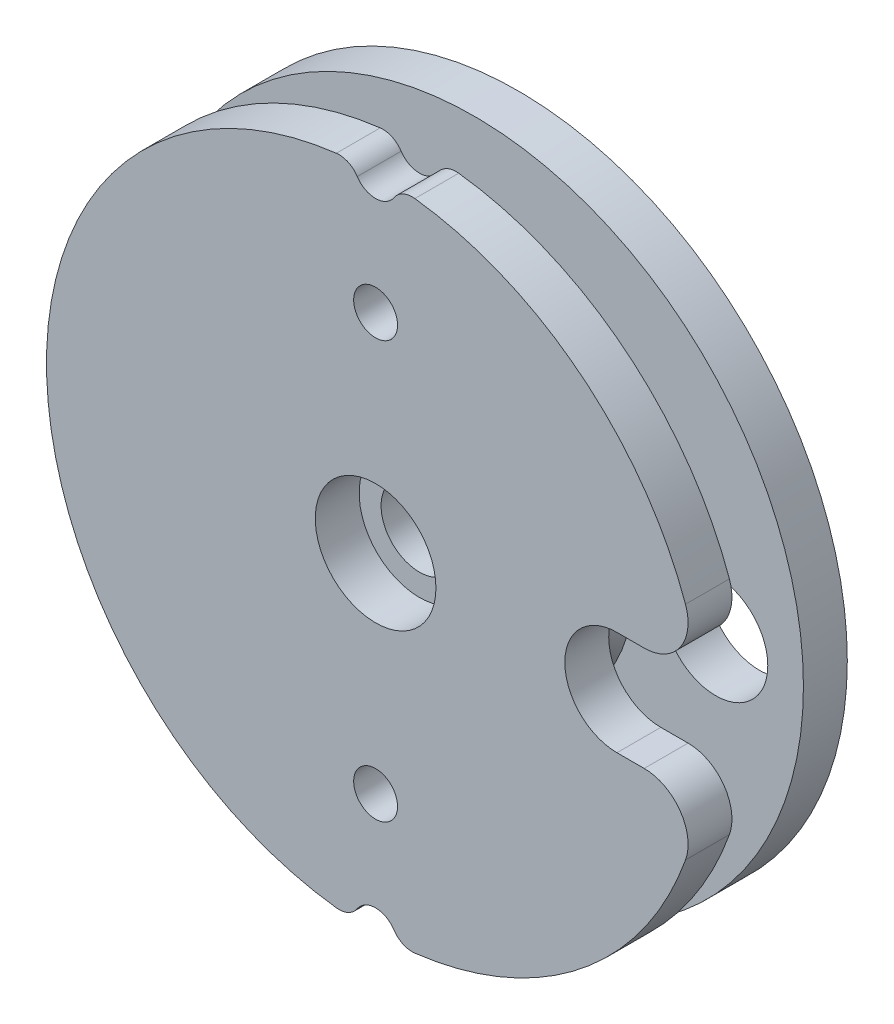
SolidWorks part; units mm, degrees
material "ABS"
ref_plane "Front Plane" through (0, 0, 0) normal (0, 0, 1) x (1, 0, 0)
ref_plane "Top Plane" through (0, 0, 0) normal (0, 1, 0) x (1, 0, 0)
ref_plane "Right Plane" through (0, 0, 0) normal (1, 0, 0) x (0, 0, -1)
sketch "Sketch1" plane through (0, 0, 0) normal (0, 0, 1) x (1, 0, 0)
  circle A0 centre (0, 0) radius 15
  dimension "D1" = 30
extrude "Body" add sketch "Sketch1" along normal mid plane 6.5
sketch "Sketch2" plane through (0, 0, 0) normal (0, 0, 1) x (1, 0, 0)
  circle A0 centre (0, 0) radius 15
  circle A1 centre (0, 0) radius 6.5
  circle A2 centre (0, 0) radius 15 construction
  dimension "D1" = 13
extrude "Pulley Clearance" cut sketch "Sketch2" against normal mid plane 2.5
sketch "Sketch3" plane through (0, 0, 3.25) normal (0, 0, 1) x (1, 0, 0)
  circle A0 centre (0, 0) radius 1.75
  dimension "D1" = 3.5
extrude "Main Bolt Through Hole" cut sketch "Sketch3" against normal through all
sketch "Sketch4" plane through (0, 0, -3.25) normal (0, 0, -1) x (-1, 0, 0)
  circle A0 centre (0, 0) radius 5.25
  dimension "D1" = 10.5
extrude "Servo Horn Clearance" cut sketch "Sketch4" against normal blind 1.8
sketch "Sketch5" plane through (0, 0, 3.25) normal (0, 0, 1) x (1, 0, 0)
  circle A0 centre (0, 0) radius 2.75
  dimension "D1" = 5.5
extrude "Main Bolt Clearance" cut sketch "Sketch5" against normal blind 2
sketch "Sketch6" plane through (0, 0, -3.25) normal (0, 0, -1) x (-1, 0, 0)
  line L0 (-15, 0) -> (15, 0) construction
  line L1 (0, 15) -> (0, -15) construction
  circle A0 centre (0, 0) radius 15 construction
  circle A1 centre (-11, 0) radius 2.375
  dimension "D1" = 4.75
  dimension "D2" = 11
extrude "Horn Attachment Holes" cut sketch "Sketch6" against normal through all
sketch "Sketch7" plane through (0, 0, 3.25) normal (0, 0, 1) x (1, 0, 0)
  line L0 (11, -2.375) -> (11, 2.375)
  line L1 (11, 2.375) -> (14.8108, 2.375)
  line L2 (11, -2.375) -> (14.8108, -2.375)
  line L3 (0, 15) -> (0, -15) construction
  circle A0 centre (11, 0) radius 2.375 construction
  circle A1 centre (0, 0) radius 15 construction
  arc A2 (14.8108, -2.375) -> (14.8108, 2.375) centre (0, 0) ccw
extrude "Horn Attachment Clearance" cut sketch "Sketch7" against normal up to surface (2 mm away) up to face at (13.375, 0, 1.25)
sketch "Sketch8" plane through (0, 0, 3.25) normal (0, 0, 1) x (1, 0, 0)
  line L0 (0, -15) -> (0, 15) construction
  line L1 (0, 0) -> (6.5, 0) construction
  circle A0 centre (0, 0) radius 6.5 construction
  circle A1 centre (0, 0) radius 6.5 construction
  circle A4 centre (0, 9.5) radius 1
  circle A5 centre (0, 15) radius 1
  circle A6 centre (0, -15) radius 1
  circle A7 centre (0, -9.5) radius 1
  arc A8 (14.8108, 2.375) -> (14.8108, -2.375) centre (0, 0) ccw construction
  point P16 (0, 6.5)
  dimension "D1" = 2
  dimension "D2" = 3
extrude "Tendon Anchor" cut sketch "Sketch8" against normal up to surface (2 mm away) up to face at (6.5, 0, 1.25)
fillet "Contouring - Bolt" radius 2 2 edges at (14.8108, 2.375, 2.25) (14.8108, -2.375, 2.25)
chamfer "Inner Chamfer" distance 0.75 angle 45 2 edges at (6.5, 0, 1.25) (6.5, 0, -1.25)
fillet "Contouring - Tendon" radius 1 4 edges at (-0.9994, 14.9667, 2.25) (0.9994, 14.9667, 2.25) (0.9994, -14.9667, 2.25) (-0.9994, -14.9667, 2.25)
sketch "Sketch9" plane through (0, 0, -3.25) normal (0, 0, -1) x (-1, 0, 0)
  line L0 (0, 0) -> (15, 0) construction
  circle A0 centre (0, 0) radius 15 construction
  circle A1 centre (11, 0) radius 1.15
  circle A2 centre (7.75, 0) radius 0.9 construction
  circle A3 centre (7.7782, -7.7782) radius 1.15
  circle A4 centre (0, -11) radius 1.15
  circle A5 centre (-7.7782, -7.7782) radius 1.15
  circle A6 centre (0, -7.75) radius 0.9 construction
  circle A7 centre (-7.7782, 7.7782) radius 1.15
  circle A8 centre (0, 11) radius 1.15
  circle A9 centre (7.7782, 7.7782) radius 1.15
  circle A10 centre (-11, 0) radius 1.15 [skipped]
  circle A12 centre (0, 7.75) radius 0.9 construction
  circle A13 centre (-7.75, 0) radius 0.9 [skipped]
  point P26 (0, 0)
  point P34 (0, 0)
  dimension "D3" = 2.3
  dimension "D4" = 1.8
  dimension "D1" = 11
  dimension "D2" = 7.75
  dimension "D5" = 8
  dimension "D6" = 4
extrude "Locking Nubs" add sketch "Sketch9" along normal blind 0.7
chamfer "Nub Chamfers" distance 0.3 angle 45 7 edges at (-1.15, -11, -3.95) (-8.9282, -7.7782, -3.95) (-12.15, 0, -3.95) (-8.9282, 7.7782, -3.95) (-1.15, 11, -3.95) (6.6282, 7.7782, -3.95) (6.6282, -7.7782, -3.95)
ref_point "Ref Center"
